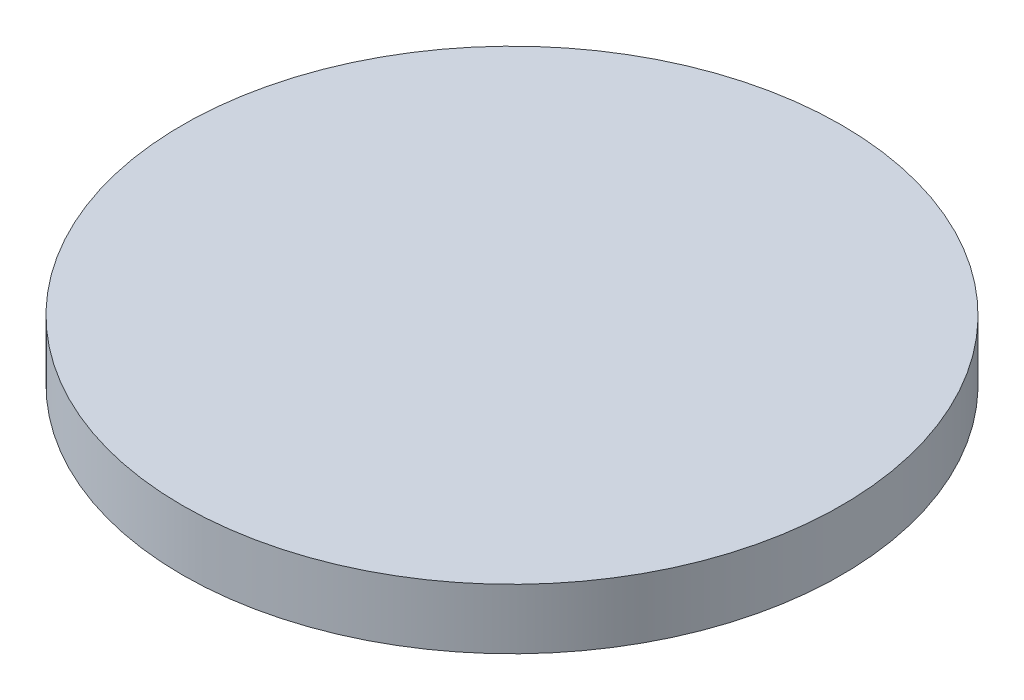
SolidWorks part; units mm, degrees
ref_plane "Front Plane" through (0, 0, 0) normal (0, 0, 1) x (1, 0, 0)
ref_plane "Top Plane" through (0, 0, 0) normal (0, 1, 0) x (1, 0, 0)
ref_plane "Right Plane" through (0, 0, 0) normal (1, 0, 0) x (0, 0, -1)
sketch "Sketch1" plane through (0, 0, 0) normal (0, 1, 0) x (1, 0, 0)
  circle A0 centre (0, 0) radius 11.5
  dimension "D1" = 23
extrude "Boss-Extrude1" add sketch "Sketch1" along normal blind 2.1
